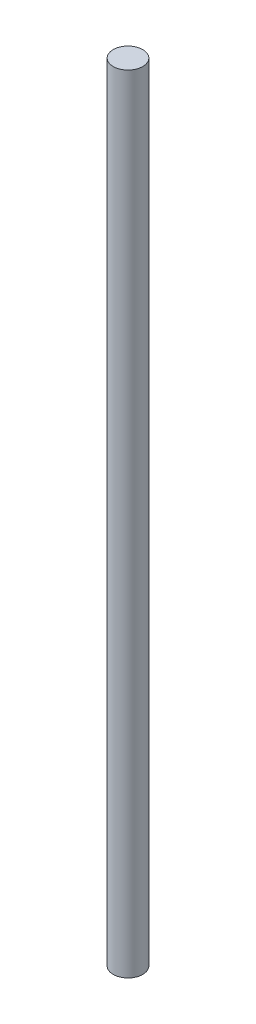
SolidWorks part; units mm, degrees
ref_plane "Front Plane" through (0, 0, 0) normal (0, 0, 1) x (1, 0, 0)
ref_plane "Top Plane" through (0, 0, 0) normal (0, 1, 0) x (1, 0, 0)
ref_plane "Right Plane" through (0, 0, 0) normal (1, 0, 0) x (0, 0, -1)
sketch "Sketch1" plane through (0, 0, 0) normal (0, 1, 0) x (1, 0, 0)
  circle A0 centre (0, 0) radius 2.3813
  dimension "D1" = 4.7625
extrude "Boss-Extrude1" add sketch "Sketch1" along normal blind 127
